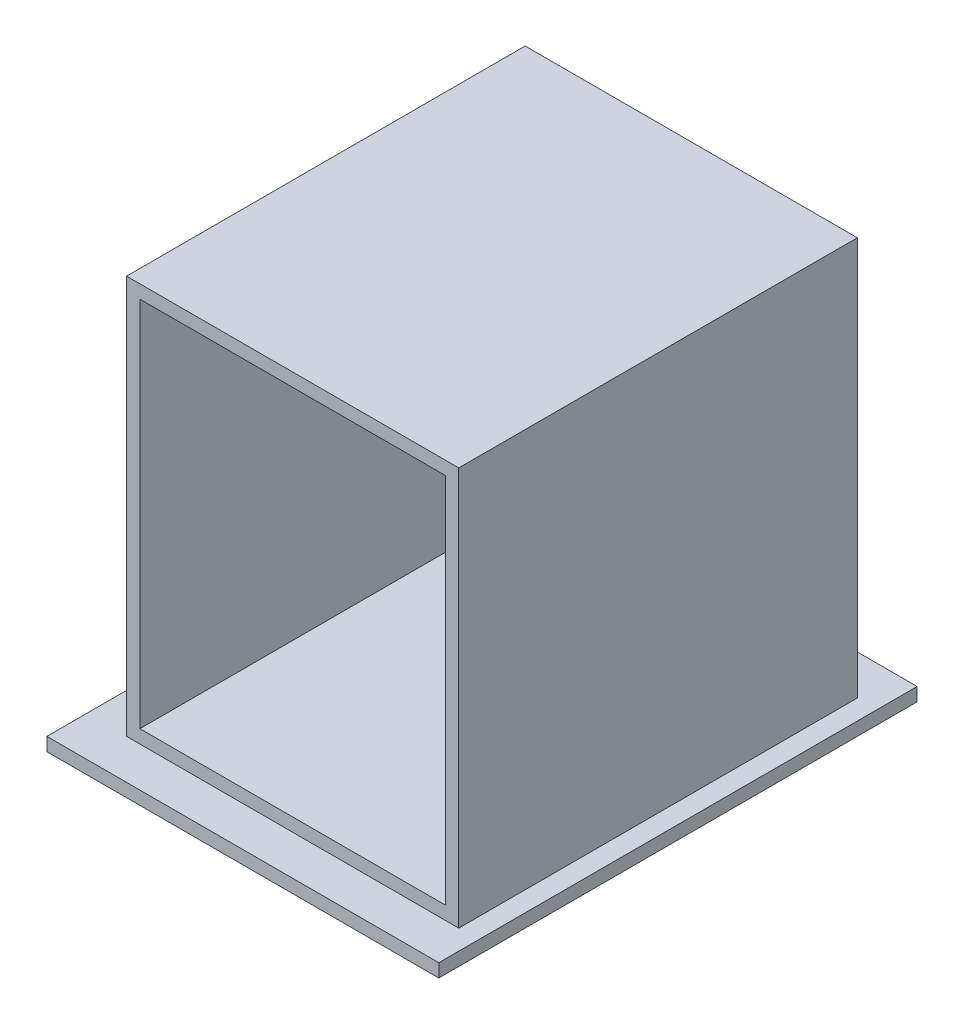
SolidWorks part; units mm, degrees
ref_plane "前视基准面" through (0, 0, 0) normal (0, 0, 1) x (1, 0, 0)
ref_plane "上视基准面" through (0, 0, 0) normal (0, 1, 0) x (1, 0, 0)
ref_plane "右视基准面" through (0, 0, 0) normal (1, 0, 0) x (0, 0, -1)
sketch "草图1" plane through (0, 0, 0) normal (0, 0, 1) x (1, 0, 0)
  line L1 (0, 0) -> (250, 0)
  line L2 (0, 0) -> (0, 300)
  line L3 (0, 300) -> (250, 300)
  line L4 (250, 0) -> (250, 300)
  dimension "D1" = 250
  dimension "D2" = 300
extrude "凸台-拉伸1" add sketch "草图1" along normal blind 300
sketch "草图2" plane through (0, 0, 300) normal (0, 0, 1) x (1, 0, 0)
  line L0 (250, 0) -> (250, 300) construction
  line L1 (10, 10) -> (240, 10)
  line L2 (10, 10) -> (10, 290)
  line L3 (10, 290) -> (240, 290)
  line L4 (240, 10) -> (240, 290)
  line L5 (250, 300) -> (0, 300) construction
  line L6 (0, 300) -> (0, 0) construction
  line L7 (0, 0) -> (250, 0) construction
  dimension "D1" = 10
  dimension "D2" = 10
  dimension "D3" = 10
  dimension "D4" = 10
extrude "切除-拉伸1" cut sketch "草图2" against normal blind 290
sketch "草图3" plane through (0, 0, 0) normal (0, -1, 0) x (1, 0, 0)
  line L0 (250, 300) -> (250, 0) construction
  line L1 (-30, 330) -> (265, 330)
  line L2 (-30, 330) -> (-30, -30)
  line L3 (-30, -30) -> (265, -30)
  line L4 (265, 330) -> (265, -30)
  line L5 (0, 300) -> (0, 0) construction
  line L6 (0, 300) -> (250, 300) construction
  line L7 (0, 0) -> (250, 0) construction
  dimension "D1" = 15
  dimension "D2" = 30
  dimension "D3" = 30
  dimension "D4" = 30
extrude "凸台-拉伸2" add sketch "草图3" along normal blind 10
sketch "草图4" plane through (0, -10, 0) normal (0, -1, 0) x (1, 0, 0)
  line L0 (75.4109, 270) -> (151.6263, 270) construction
  line L1 (75.4109, 284.2193) -> (151.6263, 284.2193)
  line L2 (75.4109, 255.7807) -> (151.6263, 255.7807)
  line L3 (265, 330) -> (-30, 330) construction
  arc A0 (75.4109, 284.2193) -> (75.4109, 255.7807) centre (75.4109, 270) ccw
  arc A1 (151.6263, 255.7807) -> (151.6263, 284.2193) centre (151.6263, 270) ccw
  point P2 (113.5186, 270)
  dimension "D1" = 60
extrude "切除-拉伸2" cut sketch "草图4" against normal blind 15 contours L1 A1 L2 A0
